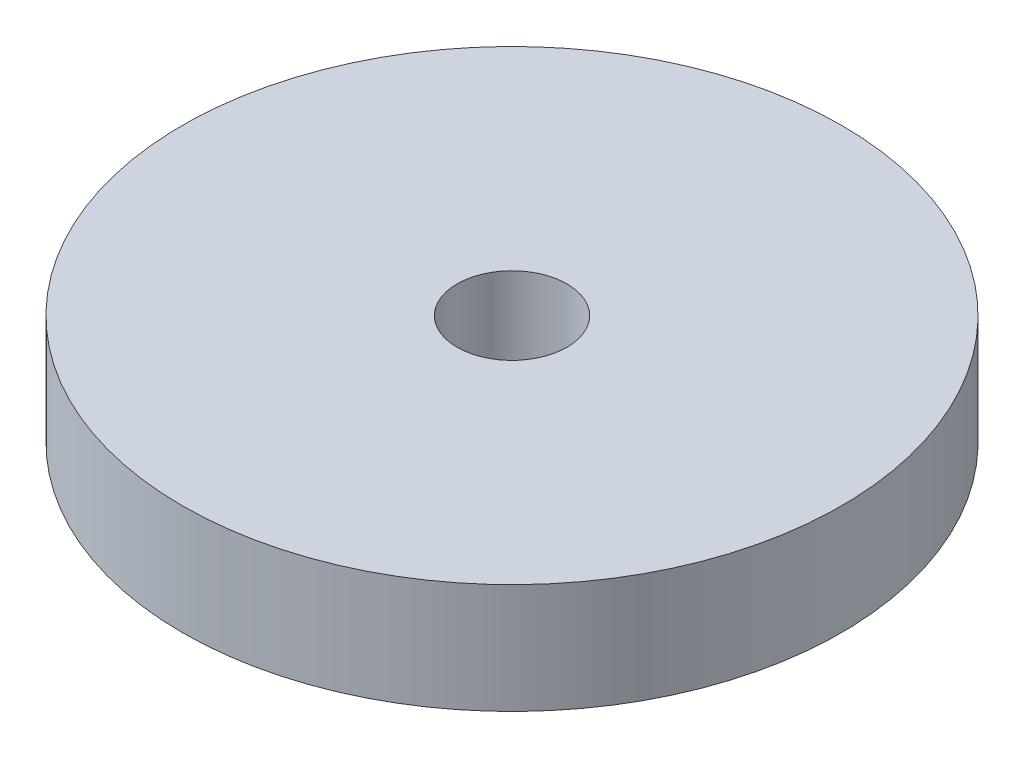
SolidWorks part; units mm, degrees
material "Plain Carbon Steel"
ref_plane "Front Plane" through (0, 0, 0) normal (0, 0, 1) x (1, 0, 0)
ref_plane "Top Plane" through (0, 0, 0) normal (0, 1, 0) x (1, 0, 0)
ref_plane "Right Plane" through (0, 0, 0) normal (1, 0, 0) x (0, 0, -1)
sketch "Sketch1" plane through (0, 0, 0) normal (0, 1, 0) x (1, 0, 0)
  circle A0 centre (0, 0) radius 9.525
  circle A1 centre (0, 0) radius 1.5875
  dimension "D1" = 3.175
  dimension "D2" = 19.05
extrude "Boss-Extrude1" add sketch "Sketch1" along normal blind 3.175
